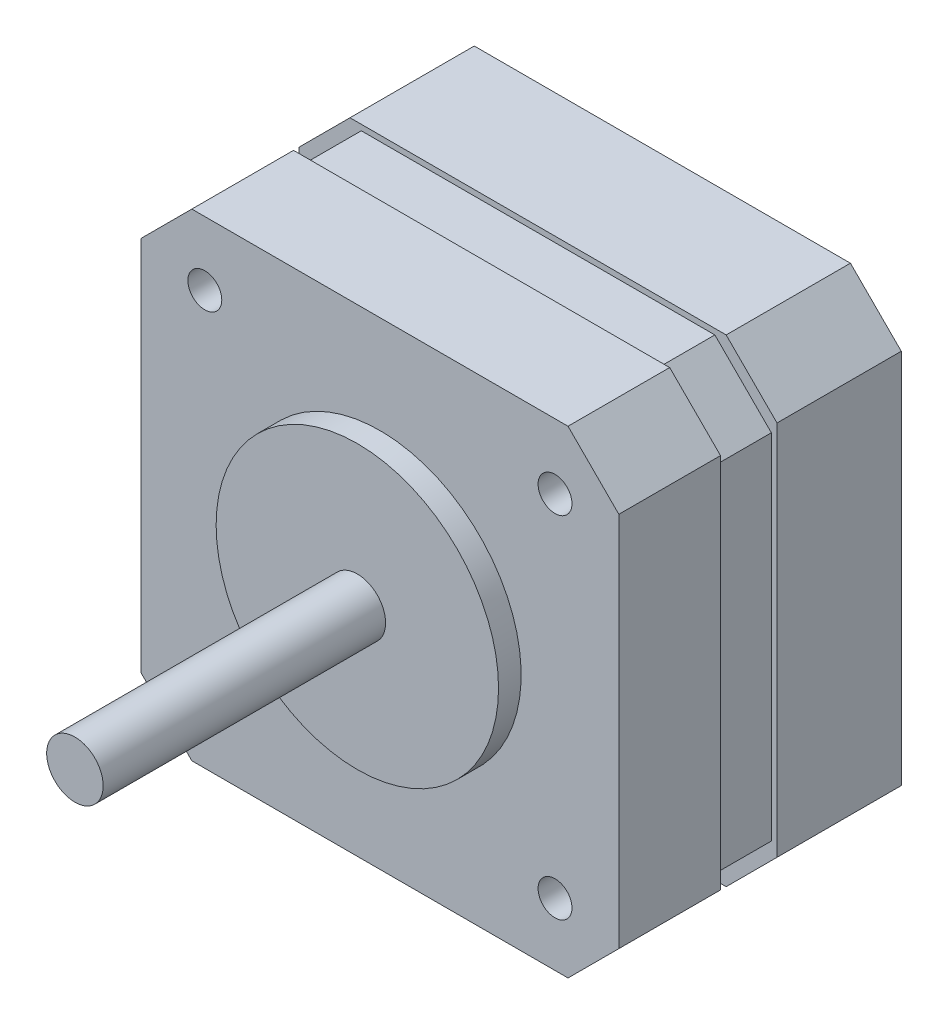
SolidWorks part; units mm, degrees
ref_plane "Plan de face" through (0, 0, 0) normal (0, 0, 1) x (1, 0, 0)
ref_plane "Plan de dessus" through (0, 0, 0) normal (0, 1, 0) x (1, 0, 0)
ref_plane "Plan de droite" through (0, 0, 0) normal (1, 0, 0) x (0, 0, -1)
sketch "Esquisse1" plane through (0, 0, 0) normal (0, 0, 1) x (1, 0, 0)
  line L1 (0, 0) -> (42.3, 0)
  line L2 (0, 0) -> (0, 42.3)
  line L3 (0, 42.3) -> (42.3, 42.3)
  line L4 (42.3, 0) -> (42.3, 42.3)
  dimension "D1" = 42.3
  dimension "D2" = 42.3
extrude "Boss.-Extru.1" add sketch "Esquisse1" along normal blind 11
sketch "Esquisse2" plane through (0, 0, 11) normal (0, 0, 1) x (1, 0, 0)
  line L0 (0, 0) -> (42.3, 0) construction
  line L1 (0.5, 0.5) -> (41.8, 0.5)
  line L2 (0.5, 0.5) -> (0.5, 41.8)
  line L3 (0.5, 41.8) -> (41.8, 41.8)
  line L4 (41.8, 0.5) -> (41.8, 41.8)
  line L5 (0, 42.3) -> (0, 0) construction
  dimension "D1" = 41.3
  dimension "D2" = 41.3
  dimension "D3" = 0.5
  dimension "D4" = 0.5
extrude "Boss.-Extru.2" add sketch "Esquisse2" along normal blind 5
sketch "Esquisse3" plane through (0, 0, 16) normal (0, 0, 1) x (1, 0, 0)
  line L1 (0, 0) -> (42.3, 0)
  line L2 (0, 0) -> (0, 42.3)
  line L3 (0, 42.3) -> (42.3, 42.3)
  line L4 (42.3, 0) -> (42.3, 42.3)
  dimension "D1" = 42.3
  dimension "D2" = 42.3
extrude "Boss.-Extru.3" add sketch "Esquisse3" along normal blind 9
sketch "Esquisse4" plane through (0, 0, 25) normal (0, 0, 1) x (1, 0, 0)
  circle A0 centre (21.15, 21.15) radius 12.5
  dimension "D1" = 25
  dimension "D2" = 21.15
  dimension "D3" = 21.15
extrude "Boss.-Extru.4" add sketch "Esquisse4" along normal blind 2
sketch "Esquisse5" plane through (0, 0, 27) normal (0, 0, 1) x (1, 0, 0)
  circle A0 centre (21.15, 21.15) radius 2.5
  dimension "D1" = 5
  dimension "D2" = 21.15
  dimension "D3" = 21.15
extrude "Boss.-Extru.5" add sketch "Esquisse5" along normal blind 25
sketch "Esquisse6" plane through (0, 0, 25) normal (0, 0, 1) x (1, 0, 0)
  line L0 (0, 0) -> (42.3, 0) construction
  line L1 (0, 42.3) -> (0, 0) construction
  circle A0 centre (5.65, 36.65) radius 1.5
  circle A1 centre (5.65, 5.65) radius 1.5
  circle A2 centre (36.65, 5.5364) radius 1.5
  circle A3 centre (36.65, 36.5364) radius 1.5
  dimension "D1" = 3
  dimension "D2" = 3
  dimension "D3" = 3
  dimension "D4" = 3
  dimension "D5" = 31
  dimension "D6" = 31
  dimension "D7" = 31
  dimension "D8" = 31
  dimension "D9" = 5.65
  dimension "D10" = 5.65
extrude "Enlèv. mat.-Extru.1" cut sketch "Esquisse6" against normal blind 15
chamfer "Chanfrein2" distance 5 angle 45 4 edges at (0.5, 0.5, 13.5) (41.8, 0.5, 13.5) (0.5, 41.8, 13.5) (41.8, 41.8, 13.5)
chamfer "Chanfrein3" distance 4.5 angle 45 8 edges at (0, 0, 5.5) (0, 0, 20.5) (42.3, 0, 5.5) (42.3, 0, 20.5) (0, 42.3, 20.5) (0, 42.3, 5.5) (42.3, 42.3, 5.5) (42.3, 42.3, 20.5)
